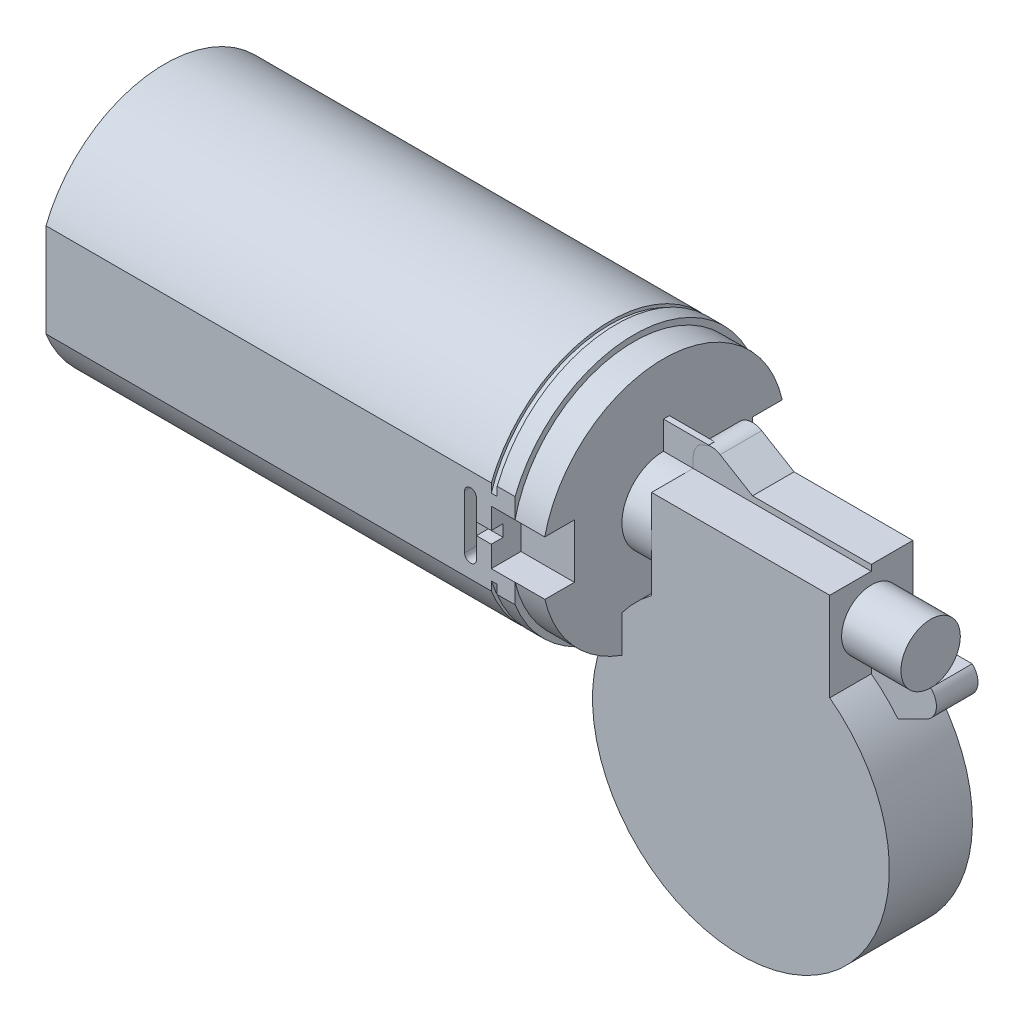
SolidWorks part; units mm, degrees
ref_plane "Plan de face" through (0, 0, 0) normal (0, 0, 1) x (1, 0, 0)
ref_plane "Plan de dessus" through (0, 0, 0) normal (0, 1, 0) x (1, 0, 0)
ref_plane "Plan de droite" through (0, 0, 0) normal (1, 0, 0) x (0, 0, -1)
sketch "Esquisse1" plane through (0, 0, 0) normal (1, 0, 0) x (0, 0, -1)
  line L0 (-35.514, 0) -> (48.2769, 0) construction
  line L1 (-20, 7.8899) -> (-20, -7.8899)
  line L2 (20, 7.8899) -> (20, -7.8899)
  arc A0 (-20, -7.8899) -> (20, -7.8899) centre (0, 0) ccw
  arc A1 (20, 7.8899) -> (-20, 7.8899) centre (0, 0) ccw
  dimension "D1" = 43
  dimension "D2" = 40
  dimension "D3" = 20
extrude "Boss.-Extru.1" add sketch "Esquisse1" along normal blind 75
sketch "Esquisse2" plane through (75, 0, 0) normal (1, 0, 0) x (0, 0, -1)
  line L0 (-20, 6.4031) -> (-20, -6.4031)
  line L1 (-20, 7.8899) -> (-20, -7.8899) construction
  line L2 (20, 6.4031) -> (20, -6.4031)
  line L3 (20, -7.8899) -> (20, 7.8899) construction
  arc A0 (-20, -6.4031) -> (20, -6.4031) centre (0, 0) ccw
  arc A1 (20, 6.4031) -> (-20, 6.4031) centre (0, 0) ccw
  dimension "D1" = 42
extrude "Boss.-Extru.2" add sketch "Esquisse2" along normal blind 1
sketch "Esquisse3" plane through (76, 0, 0) normal (1, 0, 0) x (0, 0, -1)
  line L0 (-20, 7.8899) -> (-20, -7.8899)
  line L1 (20, 7.8899) -> (20, -7.8899)
  arc A0 (20, 7.8899) -> (-20, 7.8899) centre (0, 0) ccw
  arc A1 (-20, -7.8899) -> (20, -7.8899) centre (0, 0) ccw
extrude "Boss.-Extru.3" add sketch "Esquisse3" along normal blind 3
sketch "Esquisse4" plane through (79, 0, 0) normal (1, 0, 0) x (0, 0, -1)
  line L0 (-20.0525, 4.2601) -> (-20, -4.5)
  line L1 (-20, 7.8899) -> (-20, -7.8899) construction
  line L2 (20.0525, 4.2601) -> (20.0525, -4.2601)
  arc A0 (20.0525, 4.2601) -> (-20.0525, 4.2601) centre (0, 0) ccw
  arc A1 (-20, -4.5) -> (20.0525, -4.2601) centre (0, 0) ccw
  dimension "D1" = 41
extrude "Boss.-Extru.4" add sketch "Esquisse4" along normal blind 5
sketch "Esquisse5" plane through (84, 0, 0) normal (1, 0, 0) x (0, 0, -1)
  line L0 (20, 7.8899) -> (20, -7.8899) construction
  line L1 (-20, 4.5) -> (-15, 4.5)
  line L3 (-20, -4.6168) -> (-15, -4.6168)
  line L4 (-15, 4.5) -> (-15, -4.6168)
  line L5 (20, -4.6168) -> (15, -4.6168)
  line L7 (20, 4.5) -> (15, 4.5)
  line L8 (15, -4.6168) -> (15, 4.5)
  line L10 (-20, 4.5) -> (-23.8351, 4.5)
  line L12 (-20, -4.6168) -> (-23.8351, -4.6168)
  line L13 (-23.8351, 4.5) -> (-23.8351, -4.6168)
  line L14 (20, 4.5) -> (24.0138, 4.5)
  line L16 (20, -4.6168) -> (24.0138, -4.6168)
  line L17 (24.0138, 4.5) -> (24.0138, -4.6168)
  dimension "D1" = 5
  dimension "D2" = 5
extrude "Enlèv. mat.-Extru.4" cut sketch "Esquisse5" against normal up to surface (9 mm away)
sketch "Esquisse6" plane through (0, 0, 20) normal (0, 0, 1) x (1, 0, 0)
  line L0 (71.5, -4.5584) -> (71.5, 4.4416) construction
  line L1 (70.5, -4.5584) -> (70.5, 4.4416)
  line L2 (72.5, -4.5584) -> (72.5, 4.4416)
  line L3 (75, 4.5) -> (75, -4.6168) construction
  line L4 (72.5, -0.0584) -> (64.6158, -0.0584) construction
  line L6 (72.5, 0.9416) -> (76.3438, 0.9416)
  line L7 (72.5, -1.0584) -> (72.5, -0.0584)
  line L8 (72.5, -0.0584) -> (72.5, -1.0584)
  line L9 (72.5, -1.0584) -> (76.3438, -1.0584)
  line L10 (76.3438, 0.9416) -> (76.3438, -1.0584)
  arc A0 (70.5, -4.5584) -> (72.5, -4.5584) centre (71.5, -4.5584) ccw
  arc A1 (72.5, 4.4416) -> (70.5, 4.4416) centre (71.5, 4.4416) ccw
  point P2 (71.5, -0.0584)
  line M1 (75, -4.6168) -> (75, 4.5)
  dimension "D3" = 9
  dimension "D4" = 1
  dimension "D1" = 2.5
  dimension "D2" = 2
  dimension "D5" = 1
extrude "Enlèv. mat.-Extru.5" cut sketch "Esquisse6" against normal blind 2 contours L2 A1 L1 A0 | L2 L9 L6 M1 | L10 L6 L9 M1
sketch "Esquisse7" plane through (0, 0, -20) normal (0, 0, -1) x (-1, 0, 0)
  line L0 (-71.5, 4.4416) -> (-71.5, -4.5584) construction
  line L1 (-70.5, 4.4416) -> (-70.5, -4.5584)
  line L2 (-72.5, 4.4416) -> (-72.5, -4.5584)
  line L4 (-76.3438, 0.9416) -> (-71.7336, 0.9416)
  line L5 (-76.3438, 0.9416) -> (-76.3438, -1.0584)
  line L6 (-76.3438, -1.0584) -> (-71.7336, -1.0584)
  line L7 (-71.7336, 0.9416) -> (-71.7336, -1.0584)
  line L8 (-72.5, -0.0584) -> (-64.6158, -0.0584) construction
  arc A0 (-70.5, 4.4416) -> (-72.5, 4.4416) centre (-71.5, 4.4416) ccw
  arc A1 (-72.5, -4.5584) -> (-70.5, -4.5584) centre (-71.5, -4.5584) ccw
  point P0 (-71.5, -0.0584)
  point P3 (-71.5, -0.0584)
  dimension "D1" = 2
  dimension "D2" = 1
extrude "Enlèv. mat.-Extru.7" cut sketch "Esquisse7" against normal blind 2
sketch "Esquisse8" plane through (84, 0, 0) normal (1, 0, 0) x (0, 0, -1)
  circle A0 centre (0, 0) radius 7
  dimension "D1" = 14
extrude "Boss.-Extru.5" add sketch "Esquisse8" along normal blind 35
sketch "Esquisse9" plane through (119, 0, 0) normal (1, 0, 0) x (0, 0, -1)
  circle A0 centre (0, 0) radius 5
  dimension "D1" = 10
extrude "Boss.-Extru.6" add sketch "Esquisse9" along normal blind 10
sketch3d "Esquisse3D1"
  line L1 (119, -7, 7) -> (119, -7.9669, 7)
  line L2 (119, 0, 7) -> (119, -7, 7)
  line L4 (89, 0, 7) -> (89, -7, 7)
  line L5 (89, -7, 7) -> (89, -8.0332, 7)
  line L6 (119, 0, 7) -> (119, 7, 7)
  line L7 (119, 7, 7) -> (89, 7, 7)
  line L8 (89, 0, 7) -> (89, 7, 7)
  circle A0 centre (119, 0, 0) radius 7 construction
  arc A1 (84, -4.6168, 19.9734) -> (84, -4.6168, -19.9734) centre (84, 0, 0) ccw construction
  arc A2 (89, -8.0332, 7) -> (119, -7.9669, 7) centre (104.0442, -28, 7) ccw
  point P6 (126, 0, 0)
  point P10 (104.5, 0, 0)
  point P11 (84, 0, 7)
  point P16 (104.0442, -28, 32)
  dimension "D4" = 50
  dimension "D5" = 35
  dimension "D1" = 5
  dimension "D2" = 7
  dimension "D3" = 7
extrude "Boss.-Extru.7" add sketch "Esquisse3D1" along direction (0, 0, 1) on the side against the normal blind 14 contours A2 L1 L2 L6 L7 L8 L4 L5
sketch "Esquisse10" plane through (0, 0, -7) normal (0, 0, -1) x (-1, 0, 0)
  line L0 (-99, 8) -> (-93.5435, 11.2739)
  line L1 (-89, 7) -> (-119, 7)
  line L3 (-89, 7) -> (-89, 8)
  line L4 (-89, 8) -> (-119, 8)
  line L5 (-119, 7) -> (-119, 8)
  line L6 (-89, 8.7014) -> (-89, 8)
  line L7 (-89, 14) -> (-89, 8)
  line L8 (-86.4809, 14) -> (-101.2242, 14) construction
  arc A0 (-93.5435, 11.2739) -> (-89, 8.7014) centre (-92, 8.7014) cw
  point P8 (-92, 8.7014)
  dimension "D2" = 20
  dimension "D4" = 3
  dimension "D1" = 1
  dimension "D3" = 6
extrude "Boss.-Extru.8" add sketch "Esquisse10" against normal blind 7
sketch "Esquisse11" plane through (0, 0, 0) normal (0, 0, 1) x (1, 0, 0)
  line L0 (83.0438, 11.7014) -> (91.5908, 11.7014)
  line L1 (91.5908, 7) -> (83.0438, 7)
  line L2 (83.0438, 7) -> (83.0438, 11.7014)
  line L3 (83.0438, 7) -> (83.136, 6.992)
  line L5 (83.136, 6.992) -> (91.5908, 6.992)
  line L6 (89, 7) -> (119, 7) construction
  line L7 (91.5908, 7) -> (91.5908, 11.7014)
  line L8 (83.136, 6.992) -> (83.136, 6.6344)
  line L9 (83.136, 6.6344) -> (91.5908, 6.6344)
  line L10 (91.5908, 6.992) -> (91.5908, 6.6344)
  arc A1 (93.5435, 11.2739) -> (89, 8.7014) centre (92, 8.7014) ccw construction
extrude "Boss.-Extru.14" add sketch "Esquisse11" against normal blind 1 separate body
sketch "Esquisse13" plane through (0, 0, -7) normal (0, 0, -1) x (-1, 0, 0)
  circle A0 centre (-92, 8.7014) radius 1.5
  dimension "D1" = 3
extrude "Enlèv. mat.-Extru.9" cut sketch "Esquisse13" against normal blind 5 contours A0
sketch "Esquisse14" plane through (0, 0, -7) normal (0, 0, -1) x (-1, 0, 0)
  line L0 (-119, -5) -> (-129, -5)
  line L1 (-128.3229, -9.8945) -> (-116.7358, -15.7186)
  line L2 (-116.7358, -15.7186) -> (-119, -5)
  line L3 (-129, -5) -> (-119, -5) construction
  arc A0 (-129, -5) -> (-128.3229, -9.8945) centre (-126.9756, -7.214) ccw
  point P6 (-140.1972, -7.9669)
  line M10 (-119, 8) -> (-119, -7.9669)
  arc M11 (-119, -7.9669) -> (-80.6188, -19.2678) centre (-104.0442, -28) ccw
  dimension "D2" = 3
extrude "Boss.-Extru.19" add sketch "Esquisse14" against normal blind 6 contours L0 A0 L1 M11 M10 | L1 L2 M10 M11
sketch "Esquisse15" plane through (0, 0, -1) normal (0, 0, 1) x (1, 0, 0)
  line L0 (119, -5) -> (129, -5)
  line L1 (129, -5) -> (129, -4.214)
  line L3 (129, -5) -> (129, 5) construction
  line L4 (119, -5) -> (129, -5)
  line L5 (129, -4.214) -> (116.9889, -4.214)
  line L6 (116.9889, -4.214) -> (116.7358, -15.7186)
  line L8 (116.7358, -15.7186) -> (128.3229, -9.8945)
  arc A0 (128.3229, -9.8945) -> (129, -5) centre (126.9756, -7.214) ccw
  line M1 (119, -5) -> (119, -7.9669)
  arc M2 (119, -7.9669) -> (123.5104, -12.3135) centre (104.0442, -28) cw
  line M3 (123.5104, -12.3135) -> (128.3229, -9.8945)
  arc M4 (128.3229, -9.8945) -> (129, -5) centre (126.9756, -7.214) ccw
  line M5 (129, -5) -> (119, -5)
extrude "Boss.-Extru.21" add sketch "Esquisse15" along normal blind 1 contours M5 M1 M2 M3 M4 | L6 L8 L1 L5 M2 M1 M5
